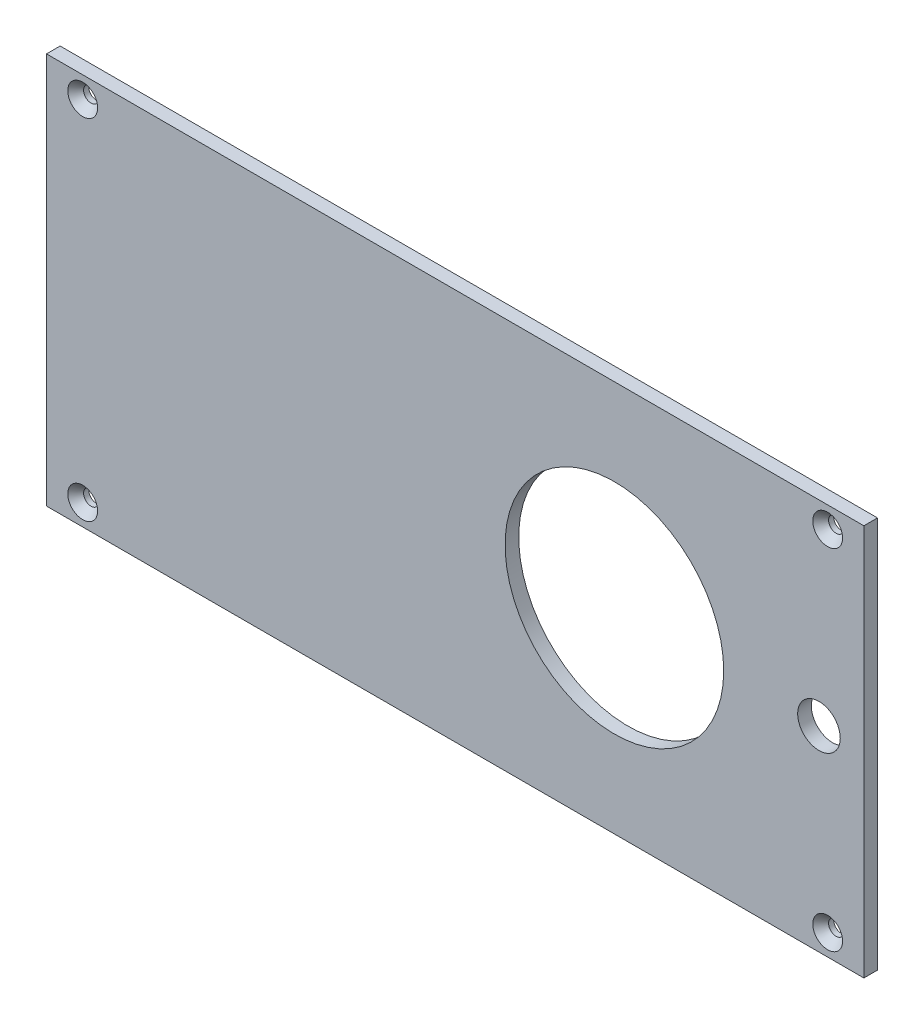
SolidWorks part; units mm, degrees
material "6061-T4 (SS)"
ref_plane "Front Plane" through (0, 0, 0) normal (0, 0, 1) x (1, 0, 0)
ref_plane "Top Plane" through (0, 0, 0) normal (0, 1, 0) x (1, 0, 0)
ref_plane "Right Plane" through (0, 0, 0) normal (1, 0, 0) x (0, 0, -1)
sketch "Sketch1" plane through (0, 0, 0) normal (0, 0, 1) x (1, 0, 0)
  line L1 (0, 0) -> (96, 0)
  line L2 (0, 0) -> (0, 46)
  line L3 (0, 46) -> (96, 46)
  line L4 (96, 0) -> (96, 46)
  dimension "D1" = 46
  dimension "D2" = 96
extrude "Boss-Extrude1" add sketch "Sketch1" along normal blind 1.6002
sketch "Sketch2" plane through (0, 0, 1.6002) normal (0, 0, 1) x (1, 0, 0)
  circle A0 centre (66.7, 23) radius 12.8397
  circle A5 centre (66.7, 23) radius 12.7 construction
  dimension "D1" = 25.6794
extrude "Cut-Extrude1" cut sketch "Sketch2" against normal through all
hole_wizard "CSK for #0 Flat Head Socket Cap Screw1" positions "Sketch6" profile "Sketch7" countersink size "#0" standard "ANSI Inch" end condition through all
sketch "Sketch6" plane through (0, 0, 1.6002) normal (0, 0, 1) x (1, 0, 0)
  line L0 (0, 46) -> (0, 0) construction
  line L1 (4.25, 43.5) -> (4.25, 2.5) construction
  line L2 (4.25, 2.5) -> (91.75, 2.5) construction
  line L3 (91.75, 2.5) -> (91.75, 43.5) construction
  line L4 (91.75, 43.5) -> (4.25, 43.5) construction
  line L6 (96, 0) -> (96, 46) construction
  line L8 (96, 46) -> (0, 46) construction
  line L9 (0, 0) -> (96, 0) construction
  point P0 (4.25, 43.5)
  point P2 (4.25, 2.5)
  point P4 (91.75, 2.5)
  point P6 (91.75, 43.5)
  dimension "D1" = 4.25
  dimension "D2" = 4.25
  dimension "D3" = 2.5
  dimension "D4" = 2.5
sketch "Sketch7" plane through (4.25, 43.5, 1.6002) normal (1, 0, 0) x (0, -1, 0)
  line L0 (0, 0) -> (0, 1.6002)
  line L1 (0, 1.6002) -> (0.889, 1.6002)
  line L2 (0.889, 1.6002) -> (0.889, 0.9935)
  line L3 (0.889, 0.9935) -> (1.7526, 0)
  line L5 (1.7526, 0) -> (0, 0)
  line L6 (-0.889, 0.9935) -> (-1.7526, 0) construction
  line L11 (0, -6.35) -> (0, 107.95) construction
  dimension "Thru Hole Dia." = 1.778
  dimension "Thru Hole Depth" = 1.6002
  dimension "Near C'Sink Dia." = 3.5052
  dimension "Near C'Sink Angle" = 82
other "AdvancedHole1" [suppressed] parameters "D1"=1.6002
sketch "Sketch12" plane through (0, 0, 1.6002) normal (0, 0, 1) x (1, 0, 0)
  point P0 (75.2, 23.05)
sketch "Sketch13" plane through (75.2, 23.05, 1.6002) normal (0, 1, 0) x (1, 0, 0)
  line L0 (0, 0) -> (0, 9.3746)
  line L1 (0, -13.1445) -> (0, 39.4335) construction
  line L2 (12.9388, 0) -> (12.9388, 1.6002)
  line L3 (0, 0) -> (12.9388, 0)
  line L4 (12.9388, 1.6002) -> (0, 9.3746)
  line L5 (-12.9388, 1.6002) -> (0, 9.3746) construction
  point P7 (0, 1.6002)
  dimension "D1" = 1.6002
  dimension "D2" = 25.8775
  dimension "D3" = 118
sketch "Sketch14" plane through (0, 0, 1.6002) normal (0, 0, 1) x (1, 0, 0)
  circle A0 centre (90.727, 23) radius 2.5
  circle A1 centre (90.727, 23) radius 1.2192 construction
  dimension "D1" = 5
extrude "Cut-Extrude2" cut sketch "Sketch14" against normal blind 10 contours A0
sketch "Sketch15" [suppressed] plane through (0, 0, 1.6002) normal (0, 0, 1) x (1, 0, 0)
  circle A0 centre (5.273, 23) radius 2.5
  circle A1 centre (5.273, 23) radius 1.2192 construction
  dimension "D1" = 5
extrude "Cut-Extrude3" [suppressed] cut sketch "Sketch15" against normal blind 10
